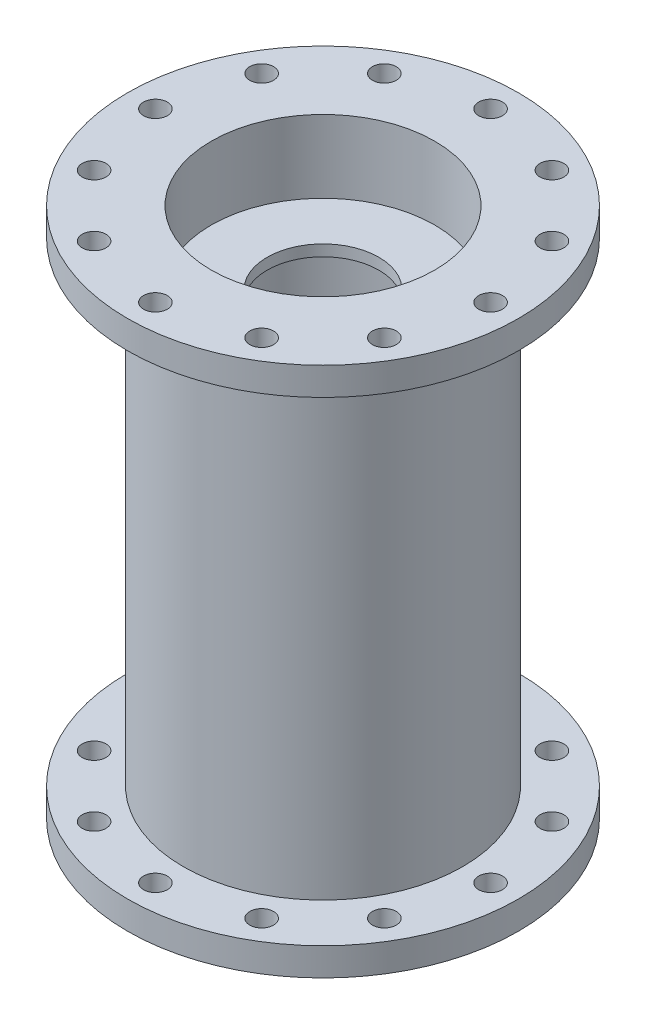
SolidWorks part; units mm, degrees
ref_plane "Front Plane" through (0, 0, 0) normal (0, 0, 1) x (1, 0, 0)
ref_plane "Top Plane" through (0, 0, 0) normal (0, 1, 0) x (1, 0, 0)
ref_plane "Right Plane" through (0, 0, 0) normal (1, 0, 0) x (0, 0, -1)
sketch "Sketch1" plane through (0, 0, 0) normal (1, 0, 0) x (0, 0, -1)
  line L1 (31.75, 6.35) -> (31.75, 114.3)
  line L8 (31.75, 120.65) -> (44.45, 120.65)
  line L9 (44.45, 120.65) -> (44.45, 114.3)
  line L10 (44.45, 114.3) -> (31.75, 114.3)
  line L11 (31.75, 0) -> (44.45, 0)
  line L12 (44.45, 0) -> (44.45, 6.35)
  line L13 (44.45, 6.35) -> (31.75, 6.35)
  line L27 (25.4, 114.3) -> (25.4, 120.65)
  line L28 (25.4, 120.65) -> (31.75, 120.65)
  line L29 (25.4, 6.35) -> (25.4, 0)
  line L30 (25.4, 0) -> (31.75, 0)
  line L31 (25.4, 114.3) -> (25.4, 6.35)
  line L32 (25.4, 0) -> (0, 0) construction
  line L33 (0, 0) -> (0, 6.35) construction
  dimension "D4" = 12.7
  dimension "D1" = 6.35
  dimension "D2" = 6.35
  dimension "D3" = 12.7
  dimension "D5" = 12.7
  dimension "D6" = 12.7
  dimension "D7" = 107.95
  dimension "D8" = 25.4
  dimension "D9" = 6.35
revolve "Chamber" add sketch "Sketch1" angle 360 about L33
sketch "Sketch4" plane through (0, 0, 0) normal (1, 0, 0) x (0, 0, -1)
  line L0 (0, 0) -> (0, 120.65) construction
  line L1 (25.4, 120.65) -> (-25.4, 120.65) construction
  line L3 (25.4, 104.14) -> (12.7, 104.14)
  line L7 (25.4, 104.14) -> (25.4, 101.6)
  line L8 (0, 60.325) -> (57.15, 60.325) construction
  line L9 (12.7, 104.14) -> (12.7, 101.6)
  line L10 (25.4, 16.51) -> (12.7, 16.51)
  line L11 (25.4, 16.51) -> (25.4, 19.05)
  line L12 (25.4, 19.05) -> (12.7, 19.05)
  line L13 (12.7, 16.51) -> (12.7, 19.05)
  line L14 (25.4, 101.6) -> (12.7, 101.6)
  line L15 (0, 0) -> (25.4, 0) construction
  line L16 (25.4, 0) -> (25.4, 16.51) construction
  point P9 (50.8, 19.05)
  point P13 (50.8, 19.05)
  point P14 (0, 0)
  point P15 (50.8, 16.51)
  point P20 (50.8, 16.51)
  point P21 (50.8, 19.05)
  dimension "D1" = 2.54
  dimension "D2" = 25.4
  dimension "D3" = 16.51
  dimension "D4" = 12.7
revolve "Turbulence Rings" add sketch "Sketch4" angle 360 about L0
sketch "Sketch5" plane through (0, 120.65, 0) normal (0, 1, 0) x (1, 0, 0)
  line L0 (0, 0) -> (-38.1, 0) construction
  line L1 (0, 0) -> (-32.9956, 19.05) construction
  circle A0 centre (0, 0) radius 38.1 construction
  point P0 (0, 0)
  point P5 (-38.1, 0)
  point P9 (-32.9956, 19.05)
  point P10 (-19.05, 32.9956)
  point P11 (0, 38.1)
  point P12 (19.05, 32.9956)
  point P13 (32.9956, 19.05)
  point P14 (38.1, 0)
  point P15 (32.9956, -19.05)
  point P16 (19.05, -32.9956)
  point P17 (0, -38.1)
  point P18 (-19.05, -32.9956)
  point P19 (-32.9956, -19.05)
  point P20 (0, 0)
  point P21 (0, 0)
  point P24 (0, 0)
  point P26 (0, 0)
  dimension "D3" = 38.1
  dimension "D1" = 30
  dimension "D2" = 12
hole_wizard "#3 (0.213) Diameter Hole3" positions "Sketch5" profile "Sketch9" hole size "#3" standard "ANSI Inch" end condition through all
sketch "Sketch9" plane through (0, 120.65, 0) normal (1, 0, 0) x (0, 0, 1)
  line L0 (0, 0) -> (0, 120.65)
  line L1 (0, 120.65) -> (2.7051, 120.65)
  line L2 (2.7051, 120.65) -> (2.7051, 0)
  line L5 (2.7051, 0) -> (0, 0)
  line L11 (0, -6.35) -> (0, 107.95) construction
  dimension "Thru Hole Dia." = 5.4102
  dimension "Thru Hole Depth" = 120.65
equation "\"Thickness of Material\"= 0.3in"
equation "\"Chamber Length\"= 4.25in"
equation "\"Flange Length\"= 0.5in"
equation "\"Chamber Wall Thickness\"= 0.25in"
equation "\"Ring Length\"= 1.2in"
equation "\"Ring Thickness\"= 0.1in"
equation "\"Number of Rings\"= 2"
equation "\"Chamber Radius\"= 1in"
equation "\"D1@Sketch4\" = \"Ring Thickness\""
equation "\"D7@Sketch1\"= \"Chamber Length\""
equation "\"D9@Sketch1\"= \"Chamber Wall Thickness\""
equation "\"D8@Sketch1\"= \"Chamber Radius\""
equation "\"Flange Thickness\"= 0.25in"
equation "\"D1@Sketch1\"= \"Flange Thickness\""
equation "\"D3@Sketch5\"= \"Chamber Radius\" + \"Chamber Wall Thickness\" + ( \"Flange to Inner Wall Length\" / 2 )"
equation "\"Flange to Inner Wall Length\"= ( \"Chamber Radius\" + \"Chamber Wall Thickness\" + \"Flange Length\" ) - ( \"Chamber Radius\" + \"Chamber Wall Thickness\" )"
equation "\"D2@Sketch4\"= \"Chamber Radius\""
equation "\"Turbulence Ring Distance from Face\"= 0.65in"
equation "\"D3@Sketch4\"= \"Turbulence Ring Distance from Face\""
equation "\"D4@Sketch1\"= \"Flange Length\""
equation "\"D3@Sketch1\"= \"Flange Length\""
equation "\"D5@Sketch1\"= \"Flange Length\""
equation "\"D6@Sketch1\"= \"Flange Length\""
